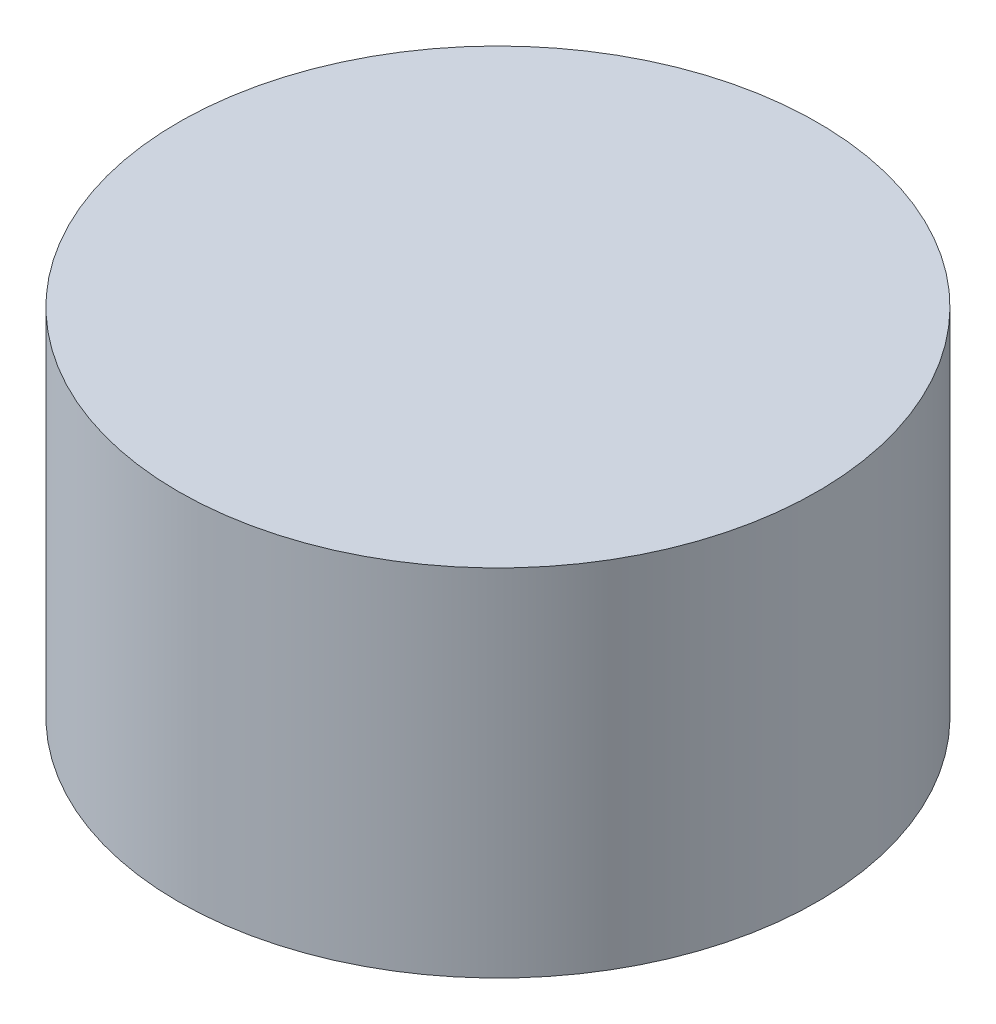
SolidWorks part; units mm, degrees
ref_plane "Piano frontale" through (0, 0, 0) normal (0, 0, 1) x (1, 0, 0)
ref_plane "Piano superiore" through (0, 0, 0) normal (0, 1, 0) x (1, 0, 0)
ref_plane "Piano destro" through (0, 0, 0) normal (1, 0, 0) x (0, 0, -1)
sketch "Sketch1" plane through (0, 0, 0) normal (0, 1, 0) x (1, 0, 0)
  circle A0 centre (0, 0) radius 13.5
  dimension "D1" = 27
extrude "Boss-Extrude1" add sketch "Sketch1" along normal blind 15
other "Save Bodies1"
